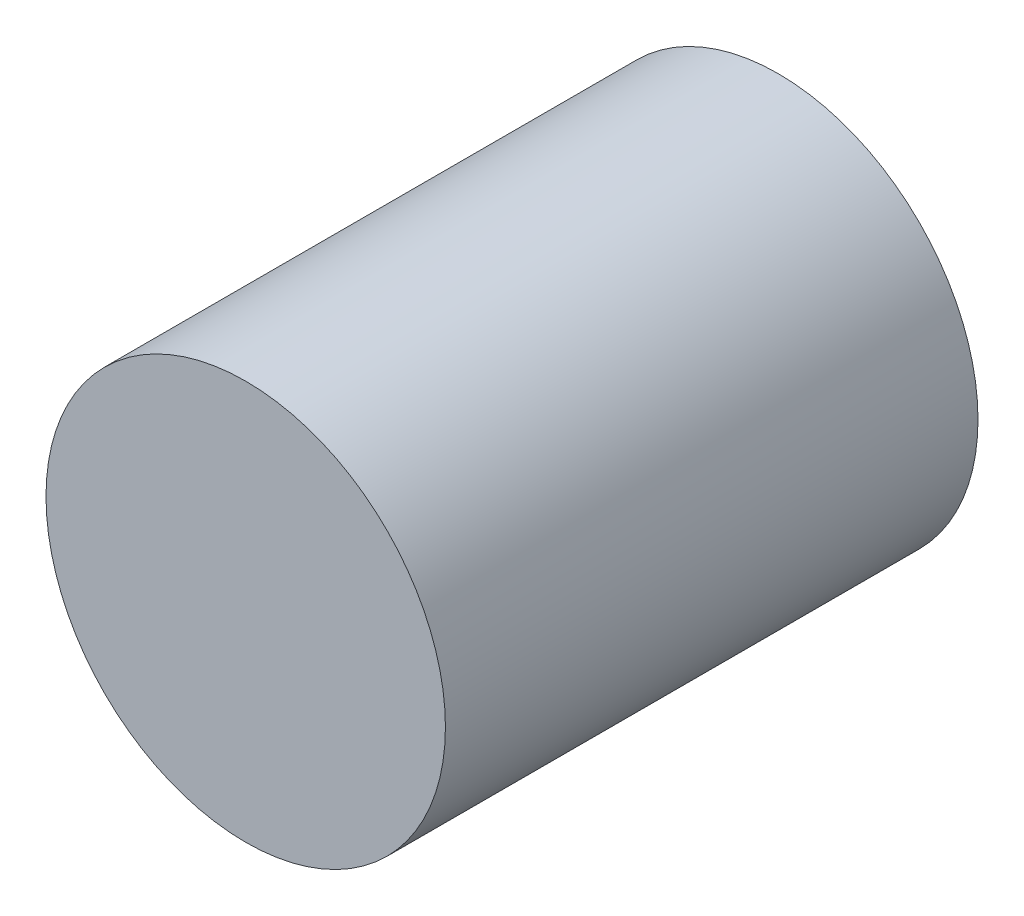
SolidWorks part; units mm, degrees
ref_plane "前视基准面" through (0, 0, 0) normal (0, 0, 1) x (1, 0, 0)
ref_plane "上视基准面" through (0, 0, 0) normal (0, 1, 0) x (1, 0, 0)
ref_plane "右视基准面" through (0, 0, 0) normal (1, 0, 0) x (0, 0, -1)
sketch "草图1" plane through (0, 0, 0) normal (0, 0, 1) x (1, 0, 0)
  circle A0 centre (0, 0) radius 1.5
  dimension "D1" = 3
extrude "凸台-拉伸1" add sketch "草图1" along normal blind 4
